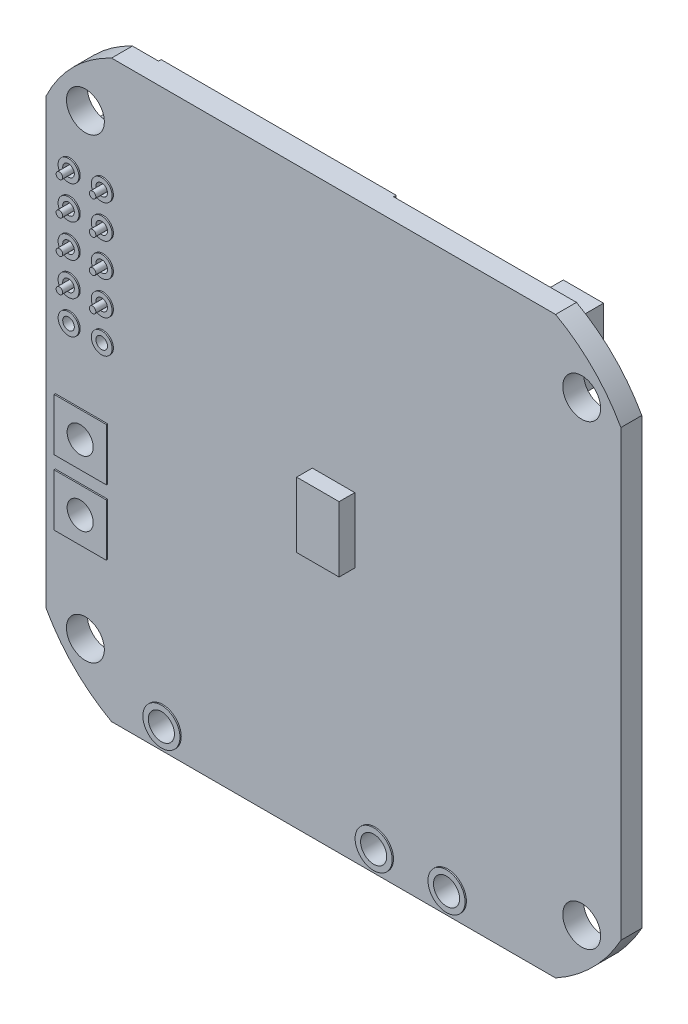
SolidWorks part; units mm, degrees
material "6061-T6 (SS)"
ref_plane "Alzado" through (0, 0, 0) normal (0, 0, 1) x (1, 0, 0)
ref_plane "Planta" through (0, 0, 0) normal (0, 1, 0) x (1, 0, 0)
ref_plane "Vista lateral" through (0, 0, 0) normal (1, 0, 0) x (0, 0, -1)
sketch "Croquis1" plane through (0, 0, 0) normal (0, 0, 1) x (1, 0, 0)
  line L0 (-22, 17) -> (-22, -17)
  line L1 (0, 0) -> (0, -6.2515) construction
  line L2 (22, 17) -> (22, -17)
  line L3 (-17, -22) -> (17, -22)
  line L4 (0, 0) -> (8.2976, 0) construction
  line L5 (-17, 22) -> (17, 22)
  arc A0 (-17, 22) -> (-22, 17) centre (-12.5089, 12.5089) ccw
  arc A2 (17, -22) -> (22, -17) centre (10.8379, -10.8379) ccw
  arc A3 (-22, -17) -> (-17, -22) centre (-10.8379, -10.8379) ccw
  arc A7 (22, 17) -> (17, 22) centre (10.8379, 10.8379) ccw
  point P0 (0, 0)
  point P4 (-22, 0)
  point P13 (0, -22)
  dimension "D3" = 21
  dimension "D4" = 34
  dimension "D1" = 34
  dimension "D2" = 22
  dimension "D5" = 22
extrude "Saliente-Extruir1" add sketch "Croquis1" along normal mid plane 1.6
sketch "Croquis2" plane through (0, 0, 0.8) normal (0, 0, 1) x (1, 0, 0)
  line L1 (19, -17.5) -> (-19, -17.5) construction
  line L2 (19, -17.5) -> (19, 17.5) construction
  line L3 (19, 17.5) -> (-19, 17.5) construction
  line L4 (-19, -17.5) -> (-19, 17.5) construction
  line L5 (19, -17.5) -> (-19, 17.5) construction
  line L6 (19, 17.5) -> (-19, -17.5) construction
  circle A0 centre (-19, 17.5) radius 1.45
  circle A1 centre (19, 17.5) radius 1.45
  circle A2 centre (19, -17.5) radius 1.45
  circle A3 centre (-19, -17.5) radius 1.45
  point P0 (0, 0)
  dimension "D1" = 2.9
  dimension "D2" = 38
  dimension "D3" = 35
extrude "Cortar-Extruir1" cut sketch "Croquis2" against normal through all
sketch "Croquis3" plane through (0, 0, 0.8) normal (0, 0, 1) x (1, 0, 0)
  line L1 (-1.625, 2.5) -> (1.625, 2.5)
  line L2 (-1.625, 2.5) -> (-1.625, -2.5)
  line L3 (-1.625, -2.5) -> (1.625, -2.5)
  line L4 (1.625, 2.5) -> (1.625, -2.5)
  line L5 (-1.625, 2.5) -> (1.625, -2.5) construction
  line L6 (-1.625, -2.5) -> (1.625, 2.5) construction
  point P0 (0, 0)
  dimension "D1" = 5
  dimension "D2" = 3.25
extrude "Saliente-Extruir2" add sketch "Croquis3" along normal blind 1.2
sketch "Croquis4" plane through (0, 0, -0.8) normal (0, 0, -1) x (-1, 0, 0)
  line L0 (22, 17) -> (22, -17) construction
  line L1 (-17, 22) -> (17, 22) construction
  circle A0 centre (17.653, 13) radius 0.445
  circle A1 centre (20.193, 13) radius 0.445
  circle A2 centre (20.193, 10.46) radius 0.445
  circle A3 centre (20.193, 7.92) radius 0.445
  circle A4 centre (20.193, 5.38) radius 0.445
  circle A5 centre (20.193, 2.84) radius 0.445
  circle A6 centre (17.653, 10.46) radius 0.445
  circle A7 centre (17.653, 7.92) radius 0.445
  circle A8 centre (17.653, 5.38) radius 0.445
  circle A9 centre (17.653, 2.84) radius 0.445
  dimension "D1" = 0.89
  dimension "D3" = 1.807
  dimension "D4" = 9
  dimension "D5" = 2.54
  dimension "D2" = 5
extrude "Cortar-Extruir2" cut sketch "Croquis4" against normal through all
sketch "Croquis5" plane through (0, 0, 0) normal (0, 0, 1) x (1, 0, 0)
  line L0 (-17, -22) -> (17, -22) construction
  line L1 (-17.3, -2.4) -> (-21.3, -2.4)
  line L2 (-17.3, -2.4) -> (-17.3, -6.4)
  line L3 (-17.3, -6.4) -> (-21.3, -6.4)
  line L4 (-21.3, -2.4) -> (-21.3, -6.4)
  line L5 (-17.3, -2.4) -> (-21.3, -6.4) construction
  line L6 (-17.3, -6.4) -> (-21.3, -2.4) construction
  line L7 (-17.3, -7.4) -> (-21.3, -7.4)
  line L8 (-17.3, -7.4) -> (-17.3, -11.4)
  line L9 (-17.3, -11.4) -> (-21.3, -11.4)
  line L10 (-21.3, -7.4) -> (-21.3, -11.4)
  line L11 (-17.3, -7.4) -> (-21.3, -11.4) construction
  line L12 (-17.3, -11.4) -> (-21.3, -7.4) construction
  line L13 (-22, 17) -> (-22, -17) construction
  circle A0 centre (-17.653, 2.84) radius 0.7974
  circle A1 centre (-20.193, 2.84) radius 0.7974
  circle A2 centre (-20.193, 5.38) radius 0.7974
  circle A3 centre (-17.653, 5.38) radius 0.7974
  circle A4 centre (-17.653, 7.92) radius 0.7974
  circle A5 centre (-17.653, 10.46) radius 0.7974
  circle A6 centre (-20.193, 7.92) radius 0.7974
  circle A7 centre (-20.193, 10.46) radius 0.7974
  circle A8 centre (-17.653, 13) radius 0.7974
  circle A9 centre (-20.193, 13) radius 0.7974
  circle A10 centre (-17.653, 13) radius 0.445
  circle A11 centre (-20.193, 13) radius 0.445
  circle A12 centre (-20.193, 10.46) radius 0.445
  circle A13 centre (-17.653, 10.46) radius 0.445
  circle A14 centre (-17.653, 7.92) radius 0.445
  circle A15 centre (-20.193, 7.92) radius 0.445
  circle A16 centre (-20.193, 5.38) radius 0.445
  circle A17 centre (-17.653, 5.38) radius 0.445
  circle A18 centre (-17.653, 2.84) radius 0.445
  circle A19 centre (-20.193, 2.84) radius 0.445
  point P0 (-19.3, -4.4)
  point P5 (-19.3, -9.4)
  dimension "D1" = 4
  dimension "D2" = 4
  dimension "D3" = 5
  dimension "D4" = 4
  dimension "D5" = 4
  dimension "D6" = 12.6
  dimension "D7" = 2.7
extrude "Saliente-Extruir3" add sketch "Croquis5" along normal mid plane 1.8
sketch "Croquis6" plane through (0, 0, -0.9) normal (0, 0, -1) x (-1, 0, 0)
  line L0 (21.3, -2.4) -> (21.3, -6.4) construction
  line L1 (21.3, -7.4) -> (21.3, -11.4) construction
  circle A0 centre (19.3, -4.4) radius 1
  circle A1 centre (19.3, -9.4) radius 1
  point P6 (21.3, -4.4)
  point P9 (21.3, -9.4)
  dimension "D1" = 2
extrude "Cortar-Extruir3" cut sketch "Croquis6" against normal through all both and the other way through all
sketch "Croquis7" plane through (0, 0, -0.8) normal (0, 0, -1) x (-1, 0, 0)
  line L0 (17, -22) -> (-17, -22) construction
  line L1 (22, 17) -> (22, -17) construction
  circle A0 centre (-8.75, -20.32) radius 1
  circle A1 centre (-3.17, -20.32) radius 1
  circle A2 centre (13.08, -20.32) radius 1
  dimension "D1" = 2
  dimension "D2" = 1.68
  dimension "D3" = 5.58
  dimension "D4" = 16.25
  dimension "D5" = 8.92
extrude "Cortar-Extruir4" cut sketch "Croquis7" against normal blind 10
sketch "Croquis8" plane through (0, 0, -0.8) normal (0, 0, -1) x (-1, 0, 0)
  line L0 (-22, -17) -> (-22, 17) construction
  line L1 (-20.5, 13.45) -> (-17.5, 13.45)
  line L2 (-20.5, 13.45) -> (-20.5, 10.95)
  line L3 (-20.5, 10.95) -> (-17.5, 10.95)
  line L4 (-17.5, 13.45) -> (-17.5, 10.95)
  line L5 (-20.5, 10.275) -> (-17.5, 10.275)
  line L6 (-20.5, 10.275) -> (-20.5, 7.775)
  line L7 (-20.5, 7.775) -> (-17.5, 7.775)
  line L8 (-17.5, 10.275) -> (-17.5, 7.775)
  line L10 (-17, 22) -> (17, 22) construction
  point P8 (-19, 7.775)
  point P11 (-20.5, 12.2)
  point P12 (-20.5, 9.025)
  point P15 (-17.5, 12.2)
  dimension "D1" = 3
  dimension "D2" = 3
  dimension "D3" = 2.5
  dimension "D4" = 3.175
  dimension "D5" = 9.8
extrude "Saliente-Extruir4" add sketch "Croquis8" along normal blind 1.2
sketch "Croquis9" plane through (0, 0, -2) normal (0, 0, -1) x (-1, 0, 0)
  line L0 (-17.5, 13.45) -> (-20.5, 13.45) construction
  line L1 (-17.5, 7.775) -> (-17.5, 10.275) construction
  line L2 (-17.5, 10.95) -> (-17.5, 13.45) construction
  circle A0 centre (-19, 12.2) radius 0.75
  circle A1 centre (-19, 9.025) radius 0.75
  point P7 (-19, 13.45)
  point P10 (-17.5, 9.025)
  point P14 (-17.5, 12.2)
  dimension "D1" = 1.5
extrude "Saliente-Extruir5" add sketch "Croquis9" along normal blind 0.8
sketch "Croquis10" plane through (0, 0, -0.8) normal (0, 0, -1) x (-1, 0, 0)
  line L0 (-22, -17) -> (-22, 17) construction
  line L1 (-16, -14.25) -> (-11, -14.25)
  line L2 (-16, -14.25) -> (-16, -19.25)
  line L3 (-16, -19.25) -> (-11, -19.25)
  line L4 (-11, -14.25) -> (-11, -19.25)
  line L5 (17, -22) -> (-17, -22) construction
  line L6 (11.25, -12.2) -> (16.25, -12.2)
  line L7 (11.25, -12.2) -> (11.25, -17.2)
  line L8 (11.25, -17.2) -> (16.25, -17.2)
  line L9 (16.25, -12.2) -> (16.25, -17.2)
  line L10 (5.8877, -14.25) -> (10.8877, -14.25)
  line L11 (5.8877, -14.25) -> (5.8877, -19.25)
  line L12 (5.8877, -19.25) -> (10.8877, -19.25)
  line L13 (10.8877, -14.25) -> (10.8877, -19.25)
  line L14 (0.4343, -14.25) -> (5.4343, -14.25)
  line L15 (0.4343, -14.25) -> (0.4343, -19.25)
  line L16 (0.4343, -19.25) -> (5.4343, -19.25)
  line L17 (5.4343, -14.25) -> (5.4343, -19.25)
  line L18 (22, 17) -> (22, -17) construction
  line L19 (-4.9483, -12.2) -> (0.0517, -12.2)
  line L20 (-4.9483, -12.2) -> (-4.9483, -17.2)
  line L21 (-4.9483, -17.2) -> (0.0517, -17.2)
  line L22 (0.0517, -12.2) -> (0.0517, -17.2)
  line L23 (-10.5433, -12.2) -> (-5.5433, -12.2)
  line L24 (-10.5433, -12.2) -> (-10.5433, -17.2)
  line L25 (-10.5433, -17.2) -> (-5.5433, -17.2)
  line L26 (-5.5433, -12.2) -> (-5.5433, -17.2)
  dimension "D1" = 5
  dimension "D2" = 5
  dimension "D3" = 6
  dimension "D4" = 2.75
  dimension "D5" = 5
  dimension "D6" = 5
  dimension "D7" = 5
  dimension "D8" = 5
  dimension "D9" = 5
  dimension "D10" = 5
  dimension "D11" = 5.75
  dimension "D12" = 4.8
  dimension "D13" = 5
  dimension "D14" = 5
  dimension "D15" = 5
  dimension "D16" = 5
extrude "Saliente-Extruir6" add sketch "Croquis10" along normal blind 0.9
sketch "Croquis11" plane through (0, 0, -0.8) normal (0, 0, -1) x (-1, 0, 0)
  line L0 (-13.6529, -19.5225) -> (-10.4593, -19.5225)
  line L1 (-10.4593, -19.5225) -> (-9.8124, -18.8756)
  line L2 (-9.8124, -18.8756) -> (-7.529, -18.8756)
  line L3 (-7.529, -18.8756) -> (-7.1476, -19.257)
  line L4 (-7.1476, -19.257) -> (-7.1476, -21.3437)
  line L5 (-7.1476, -21.3437) -> (-7.529, -21.7251)
  line L6 (-7.529, -21.7251) -> (-13.8301, -21.7251)
  line L7 (-13.8301, -21.7251) -> (-14.1414, -21.4138)
  line L8 (-14.1414, -21.4138) -> (-14.1414, -20.011)
  line L9 (-14.1414, -20.011) -> (-13.6529, -19.5225)
  line L10 (8.1723, -19.5225) -> (11.1983, -19.5225)
  line L11 (11.1983, -19.5225) -> (12.0225, -18.6983)
  line L12 (12.0225, -18.6983) -> (14.2962, -18.6983)
  line L13 (14.2962, -18.6983) -> (14.7785, -19.1806)
  line L14 (14.7785, -19.1806) -> (14.7785, -21.2429)
  line L15 (14.7785, -21.2429) -> (14.2962, -21.7251)
  line L16 (14.2962, -21.7251) -> (7.9951, -21.7251)
  line L17 (7.9951, -21.7251) -> (7.6839, -21.4138)
  line L18 (7.6839, -21.4138) -> (7.6839, -20.011)
  line L19 (7.6839, -20.011) -> (8.1723, -19.5225)
  line L20 (2.2631, -20.011) -> (1.7746, -19.5225)
  line L21 (2.2631, -21.4138) -> (2.2631, -20.011)
  line L22 (1.9518, -21.7251) -> (2.2631, -21.4138)
  line L23 (-4.3493, -21.7251) -> (1.9518, -21.7251)
  line L24 (-4.7307, -21.3437) -> (-4.3493, -21.7251)
  line L25 (-4.7307, -19.257) -> (-4.7307, -21.3437)
  line L26 (-4.3493, -18.8756) -> (-4.7307, -19.257)
  line L27 (-2.0659, -18.8756) -> (-4.3493, -18.8756)
  line L28 (-1.4189, -19.5225) -> (-2.0659, -18.8756)
  line L29 (1.7746, -19.5225) -> (-1.4189, -19.5225)
  line L30 (-5.9391, -18.0693) -> (-5.9391, -23.1735) construction
  circle A0 centre (-8.75, -20.32) radius 1
  circle A1 centre (-3.17, -20.32) radius 1
  circle A2 centre (13.08, -20.32) radius 1
extrude "Saliente-Extruir7" add sketch "Croquis11" along normal blind 0.1
sketch "Croquis12" plane through (0, 0, -0.8) normal (0, 0, -1) x (-1, 0, 0)
  line L0 (-19.5752, -2.7898) -> (-13.4845, -8.8805)
  line L1 (-19.5752, -2.7898) -> (-13.4845, 3.301)
  line L2 (-13.4845, -8.8805) -> (-7.3937, -2.7898)
  line L3 (-13.4845, 3.301) -> (-7.3937, -2.7898)
  line L4 (17, -22) -> (-17, -22) construction
  dimension "D1" = 45
extrude "Saliente-Extruir8" add sketch "Croquis12" along normal blind 0.75
sketch "Croquis13" plane through (0, 0, -0.8) normal (0, 0, -1) x (-1, 0, 0)
  line L1 (-16.4217, 20.3319) -> (-13.3413, 20.3319)
  line L2 (-16.4217, 20.3319) -> (-16.4217, 15.0982)
  line L3 (-16.4217, 15.0982) -> (-13.3413, 15.0982)
  line L4 (-13.3413, 20.3319) -> (-13.3413, 15.0982)
extrude "Saliente-Extruir9" add sketch "Croquis13" along normal blind 2.65
sketch "Croquis14" plane through (0, 0, -0.8) normal (0, 0, -1) x (-1, 0, 0)
  line L1 (-12.0511, 17.4084) -> (-8.2311, 17.4084)
  line L2 (-12.0511, 17.4084) -> (-12.0511, 13.5884)
  line L3 (-12.0511, 13.5884) -> (-8.2311, 13.5884)
  line L4 (-8.2311, 17.4084) -> (-8.2311, 13.5884)
  dimension "D1" = 3.82
extrude "Saliente-Extruir10" add sketch "Croquis14" along normal blind 3
sketch "Croquis30" plane through (0, 0, 0.8) normal (0, 0, 1) x (1, 0, 0)
  circle A0 centre (-13.08, -20.32) radius 1.4199
  circle A1 centre (8.75, -20.32) radius 1.4199
  circle A2 centre (3.17, -20.32) radius 1.4199
  circle A3 centre (-13.08, -20.32) radius 1
  circle A4 centre (3.17, -20.32) radius 1
  circle A5 centre (8.75, -20.32) radius 1
extrude "Saliente-Extruir17" add sketch "Croquis30" along normal blind 0.1
sketch "Croquis29" plane through (0, 0, -0.8) normal (0, 0, -1) x (-1, 0, 0)
  line L0 (-17, 22) -> (17, 22) construction
  line L1 (10.5, 1.5) -> (14, 1.5)
  line L2 (10.5, 1.5) -> (10.5, 0)
  line L3 (10.5, 0) -> (14, 0)
  line L4 (14, 1.5) -> (14, 0)
  line L5 (10.5, -0.65) -> (14, -0.65)
  line L6 (10.5, -0.65) -> (10.5, -2.15)
  line L7 (10.5, -2.15) -> (14, -2.15)
  line L8 (14, -0.65) -> (14, -2.15)
  line L9 (2.75, 1.5) -> (6.25, 1.5)
  line L10 (2.75, 1.5) -> (2.75, 0)
  line L11 (2.75, 0) -> (6.25, 0)
  line L12 (6.25, 1.5) -> (6.25, 0)
  line L13 (22, 17) -> (22, -17) construction
  dimension "D1" = 3.5
  dimension "D2" = 1.5
  dimension "D3" = 0.65
  dimension "D4" = 3.5
  dimension "D5" = 20.5
  dimension "D6" = 11.5
  dimension "D7" = 7.75
extrude "Saliente-Extruir16" add sketch "Croquis29" along normal blind 0.5
sketch "Croquis31" plane through (0, 0, -0.8) normal (0, 0, -1) x (-1, 0, 0)
  line L0 (-17, 22) -> (17, 22) construction
  line L1 (-3, 22) -> (15, 22)
  line L2 (-3, 22) -> (-3, 2.65)
  line L3 (-3, 2.65) -> (15, 2.65)
  line L4 (15, 22) -> (15, 2.65)
  line L5 (22, 17) -> (22, -17) construction
  dimension "D1" = 19.35
  dimension "D2" = 18
  dimension "D3" = 7
extrude "Boss-Extrude1" add sketch "Croquis31" along normal blind 0.2
chamfer "Chaflán1" distance 1 angle 45 4 edges at (12.0511, 17.4084, -2.3) (8.2311, 17.4084, -2.3) (12.0511, 13.5884, -2.3) (8.2311, 13.5884, -2.3)
sketch "Croquis32" plane through (0, 0, -0.9) normal (0, 0, -1) x (-1, 0, 0)
  circle A0 centre (17.653, 13) radius 0.65
  circle A1 centre (20.193, 13) radius 0.65
  circle A2 centre (20.193, 10.46) radius 0.65
  circle A3 centre (17.653, 10.46) radius 0.65
  circle A4 centre (17.653, 7.92) radius 0.65
  circle A5 centre (20.193, 7.92) radius 0.65
  circle A6 centre (20.193, 5.38) radius 0.65
  circle A7 centre (17.653, 5.38) radius 0.65
  dimension "D1" = 1.3
extrude "Saliente-Extruir18" add sketch "Croquis32" along normal blind 1.6
sketch "Croquis33" plane through (0, 0, -0.9) normal (0, 0, 1) x (1, 0, 0)
  circle A0 centre (-20.193, 13) radius 0.25
  circle A1 centre (-17.653, 13) radius 0.25
  circle A2 centre (-17.653, 10.46) radius 0.25
  circle A3 centre (-20.193, 10.46) radius 0.25
  circle A4 centre (-20.193, 7.92) radius 0.25
  circle A5 centre (-17.653, 7.92) radius 0.25
  circle A6 centre (-17.653, 5.38) radius 0.25
  circle A7 centre (-20.193, 5.38) radius 0.25
  dimension "D1" = 0.5
extrude "Saliente-Extruir19" add sketch "Croquis33" along normal blind 2.5
sketch "Croquis34" plane through (0, 0, -2.5) normal (0, 0, -1) x (-1, 0, 0)
  line L0 (16.388, 14.1102) -> (16.388, 11.9202)
  line L1 (16.388, 11.9202) -> (16.8728, 11.735)
  line L2 (16.8728, 11.735) -> (18.4226, 11.735)
  line L3 (18.4226, 11.735) -> (18.918, 11.8898)
  line L4 (18.918, 11.8898) -> (18.918, 14.1102)
  line L5 (18.918, 14.1102) -> (18.4332, 14.265)
  line L6 (18.4332, 14.265) -> (16.8728, 14.265)
  line L7 (16.8728, 14.265) -> (16.388, 14.1102)
  line L8 (17.653, 13) -> (17.653, 14.4547) construction
  line L9 (17.653, 13) -> (15.9852, 13) construction
  line L10 (18.928, 14.1102) -> (18.928, 11.9202)
  line L11 (18.928, 11.9202) -> (19.4128, 11.735)
  line L12 (19.4128, 11.735) -> (20.9626, 11.735)
  line L13 (20.9626, 11.735) -> (21.458, 11.8898)
  line L14 (21.458, 11.8898) -> (21.458, 14.1102)
  line L15 (21.458, 14.1102) -> (20.9732, 14.265)
  line L16 (20.9732, 14.265) -> (19.4128, 14.265)
  line L17 (19.4128, 14.265) -> (18.928, 14.1102)
  line L18 (20.193, 13) -> (20.193, 14.4547) construction
  line L19 (20.193, 13) -> (18.5252, 13) construction
  line L20 (18.928, 11.5702) -> (18.928, 9.3802)
  line L21 (18.928, 9.3802) -> (19.4128, 9.195)
  line L22 (19.4128, 9.195) -> (20.9626, 9.195)
  line L23 (20.9626, 9.195) -> (21.458, 9.3498)
  line L24 (21.458, 9.3498) -> (21.458, 11.5702)
  line L25 (21.458, 11.5702) -> (20.9732, 11.725)
  line L26 (20.9732, 11.725) -> (19.4128, 11.725)
  line L27 (19.4128, 11.725) -> (18.928, 11.5702)
  line L28 (20.193, 10.46) -> (20.193, 11.9147) construction
  line L29 (20.193, 10.46) -> (18.5252, 10.46) construction
  line L30 (16.388, 11.5702) -> (16.388, 9.3802)
  line L31 (16.388, 9.3802) -> (16.8728, 9.195)
  line L32 (16.8728, 9.195) -> (18.4226, 9.195)
  line L33 (18.4226, 9.195) -> (18.918, 9.3498)
  line L34 (18.918, 9.3498) -> (18.918, 11.5702)
  line L35 (18.918, 11.5702) -> (18.4332, 11.725)
  line L36 (18.4332, 11.725) -> (16.8728, 11.725)
  line L37 (16.8728, 11.725) -> (16.388, 11.5702)
  line L38 (17.653, 10.46) -> (17.653, 11.9147) construction
  line L39 (17.653, 10.46) -> (15.9852, 10.46) construction
  line L40 (16.388, 9.0302) -> (16.388, 6.8402)
  line L41 (16.388, 6.8402) -> (16.8728, 6.655)
  line L42 (16.8728, 6.655) -> (18.4226, 6.655)
  line L43 (18.4226, 6.655) -> (18.918, 6.8098)
  line L44 (18.918, 6.8098) -> (18.918, 9.0302)
  line L45 (18.918, 9.0302) -> (18.4332, 9.185)
  line L46 (18.4332, 9.185) -> (16.8728, 9.185)
  line L47 (16.8728, 9.185) -> (16.388, 9.0302)
  line L48 (17.653, 7.92) -> (17.653, 9.3747) construction
  line L49 (17.653, 7.92) -> (15.9852, 7.92) construction
  line L50 (18.928, 9.0302) -> (18.928, 6.8402)
  line L51 (18.928, 6.8402) -> (19.4128, 6.655)
  line L52 (19.4128, 6.655) -> (20.9626, 6.655)
  line L53 (20.9626, 6.655) -> (21.458, 6.8098)
  line L54 (21.458, 6.8098) -> (21.458, 9.0302)
  line L55 (21.458, 9.0302) -> (20.9732, 9.185)
  line L56 (20.9732, 9.185) -> (19.4128, 9.185)
  line L57 (19.4128, 9.185) -> (18.928, 9.0302)
  line L58 (20.193, 7.92) -> (20.193, 9.3747) construction
  line L59 (20.193, 7.92) -> (18.5252, 7.92) construction
  line L60 (16.388, 6.4902) -> (16.388, 4.3002)
  line L61 (16.388, 4.3002) -> (16.8728, 4.115)
  line L62 (16.8728, 4.115) -> (18.4226, 4.115)
  line L63 (18.4226, 4.115) -> (18.918, 4.2698)
  line L64 (18.918, 4.2698) -> (18.918, 6.4902)
  line L65 (18.918, 6.4902) -> (18.4332, 6.645)
  line L66 (18.4332, 6.645) -> (16.8728, 6.645)
  line L67 (16.8728, 6.645) -> (16.388, 6.4902)
  line L68 (17.653, 5.38) -> (17.653, 6.8347) construction
  line L69 (17.653, 5.38) -> (15.9852, 5.38) construction
  line L70 (18.928, 6.4902) -> (18.928, 4.3002)
  line L71 (18.928, 4.3002) -> (19.4128, 4.115)
  line L72 (19.4128, 4.115) -> (20.9626, 4.115)
  line L73 (20.9626, 4.115) -> (21.458, 4.2698)
  line L74 (21.458, 4.2698) -> (21.458, 6.4902)
  line L75 (21.458, 6.4902) -> (20.9732, 6.645)
  line L76 (20.9732, 6.645) -> (19.4128, 6.645)
  line L77 (19.4128, 6.645) -> (18.928, 6.4902)
  line L78 (20.193, 5.38) -> (20.193, 6.8347) construction
  line L79 (20.193, 5.38) -> (18.5252, 5.38) construction
  circle A0 centre (17.653, 13) radius 0.65
  circle A1 centre (20.193, 13) radius 0.64
  circle A2 centre (20.193, 10.46) radius 0.6641
  circle A3 centre (17.653, 10.46) radius 0.65
  circle A4 centre (17.653, 7.92) radius 0.65
  circle A5 centre (20.193, 7.92) radius 0.65
  circle A6 centre (20.193, 5.38) radius 0.65
  circle A7 centre (17.653, 5.38) radius 0.65
  circle A8 centre (17.653, 10.46) radius 0.65 construction
  point P2 (17.653, 14.265)
  point P9 (18.918, 13)
  dimension "D1" = 2.53
  dimension "D2" = 2.53
  dimension "D3" = 2
  dimension "D4" = 4
extrude "Saliente-Extruir20" add sketch "Croquis34" along normal blind 3
